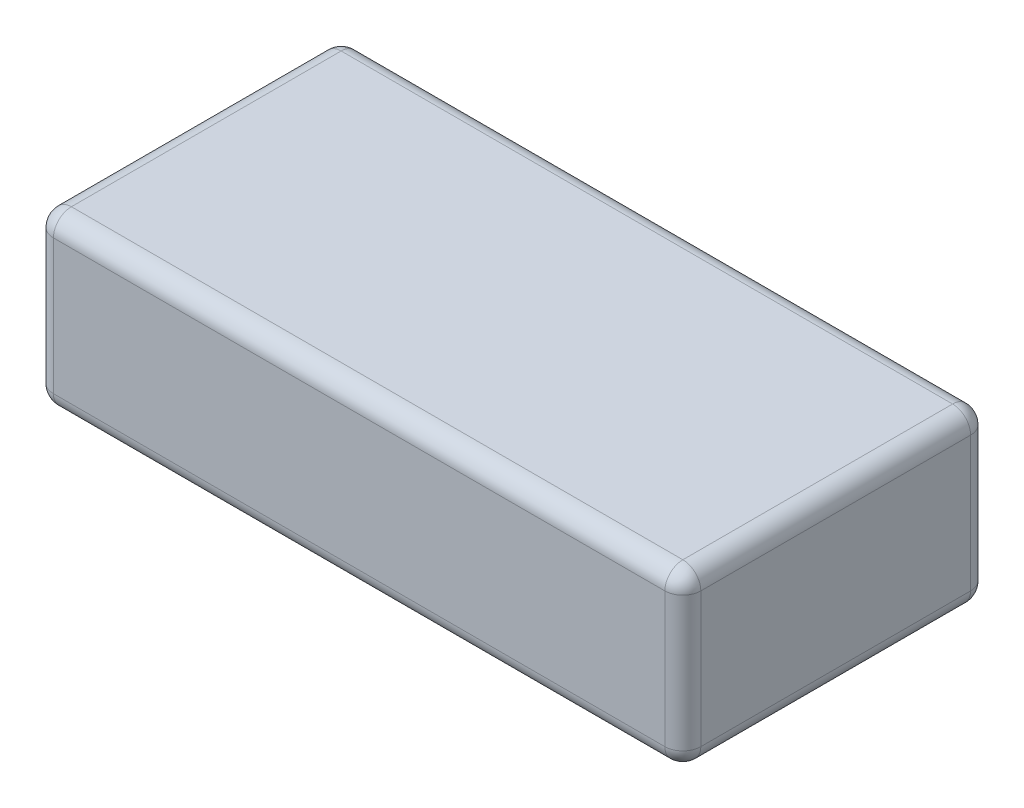
SolidWorks part; units mm, degrees
material "Alumina"
ref_plane "Front Plane" through (0, 0, 0) normal (0, 0, 1) x (1, 0, 0)
ref_plane "Top Plane" through (0, 0, 0) normal (0, 1, 0) x (1, 0, 0)
ref_plane "Right Plane" through (0, 0, 0) normal (1, 0, 0) x (0, 0, -1)
sketch "Sketch1" plane through (0, 0, 0) normal (0, 1, 0) x (1, 0, 0)
  line L1 (-36, -17) -> (36, -17)
  line L2 (-36, -17) -> (-36, 17)
  line L3 (-36, 17) -> (36, 17)
  line L4 (36, -17) -> (36, 17)
  line L5 (-36, -17) -> (36, 17) construction
  line L6 (-36, 17) -> (36, -17) construction
  point P0 (0, 0)
  dimension "D1" = 72
  dimension "D2" = 34
extrude "Boss-Extrude1" add sketch "Sketch1" along normal blind 19
fillet "Fillet1" radius 2 12 edges at (0, 0, -17) (36, 9.5, -17) (36, 0, 0) (-36, 9.5, -17) (-36, 0, 0) (-36, 9.5, 17) (36, 9.5, 17) (0, 0, 17) (0, 19, 17) (-36, 19, 0) (0, 19, -17) (36, 19, 0)
